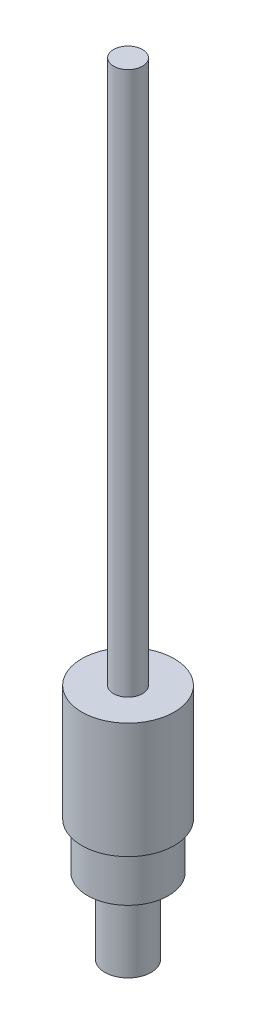
SolidWorks part; units mm, degrees
material "Acero al carbono no aleado"
ref_plane "Alzado" through (0, 0, 0) normal (0, 0, 1) x (1, 0, 0)
ref_plane "Planta" through (0, 0, 0) normal (0, 1, 0) x (1, 0, 0)
ref_plane "Vista lateral" through (0, 0, 0) normal (1, 0, 0) x (0, 0, -1)
sketch "Croquis1" plane through (0, 0, 0) normal (0, 0, 1) x (1, 0, 0)
  line L0 (0, 0) -> (-4, 0)
  line L1 (-4, 0) -> (-4, 13)
  line L2 (-4, 13) -> (-7, 13)
  line L3 (-7, 13) -> (-7, 21)
  line L4 (-7, 21) -> (-8, 21)
  line L5 (0, 0) -> (0, 150.6194) construction
  line L6 (-8, 21) -> (-8, 41)
  line L7 (-8, 41) -> (-2.5, 41)
  line L8 (-2.5, 41) -> (-2.5, 135)
  line L9 (-2.5, 135) -> (0, 135)
  line L10 (0, 0) -> (0, 135)
  dimension "D1" = 4
  dimension "D2" = 13
  dimension "D3" = 7
  dimension "D4" = 21
  dimension "D5" = 8
  dimension "D6" = 41
  dimension "D7" = 135
  dimension "D8" = 2.5
revolve "Revolución1" add sketch "Croquis1" angle 360 about L5
